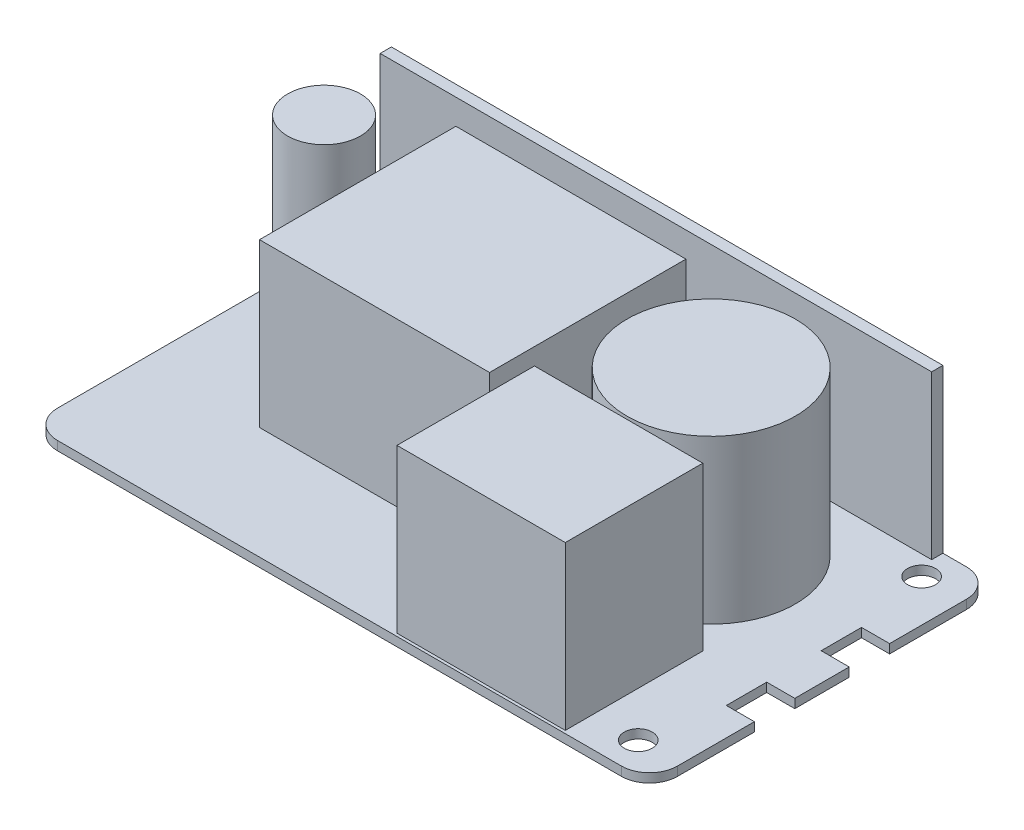
SolidWorks part; units mm, degrees
ref_plane "前视基准面" through (0, 0, 0) normal (0, 0, 1) x (1, 0, 0)
ref_plane "上视基准面" through (0, 0, 0) normal (0, 1, 0) x (1, 0, 0)
ref_plane "右视基准面" through (0, 0, 0) normal (1, 0, 0) x (0, 0, -1)
sketch "草图1" plane through (0, 0, 0) normal (0, 1, 0) x (1, 0, 0)
  line L0 (55.25, 12.05) -> (50.25, 12.05)
  line L1 (-50.25, 30.75) -> (50.25, 30.75)
  line L2 (-55.25, 25.75) -> (-55.25, -25.75)
  line L3 (-50.25, -30.75) -> (50.25, -30.75)
  line L4 (55.25, 25.75) -> (55.25, 12.05)
  line L5 (-55.25, 30.75) -> (55.25, -30.75) construction
  line L6 (-55.25, -30.75) -> (55.25, 30.75) construction
  line L7 (50.25, 12.05) -> (50.25, 4.85)
  line L8 (50.25, 4.85) -> (55.25, 4.85)
  line L9 (67.1485, 0) -> (0, 0) construction
  line L10 (50.25, -4.85) -> (55.25, -4.85)
  line L11 (50.25, -12.05) -> (50.25, -4.85)
  line L12 (55.25, -12.05) -> (50.25, -12.05)
  line L13 (55.25, 4.85) -> (55.25, -4.85)
  line L14 (55.25, -12.05) -> (55.25, -25.75)
  arc A0 (50.25, 30.75) -> (55.25, 25.75) centre (50.25, 25.75) cw
  arc A1 (50.25, -30.75) -> (55.25, -25.75) centre (50.25, -25.75) ccw
  arc A2 (-55.25, -25.75) -> (-50.25, -30.75) centre (-50.25, -25.75) ccw
  arc A3 (-50.25, 30.75) -> (-55.25, 25.75) centre (-50.25, 25.75) ccw
  point P0 (0, 0)
  dimension "D3" = 5
  dimension "D1" = 110.5
  dimension "D2" = 61.5
  dimension "D4" = 18.7
  dimension "D5" = 5
  dimension "D6" = 7.2
extrude "凸台-拉伸1" add sketch "草图1" along normal blind 1.6
sketch "草图2" plane through (0, 1.6, 0) normal (0, 1, 0) x (1, 0, 0)
  line L0 (55.25, 12.05) -> (55.25, 25.75) construction
  line L2 (50.25, 30.75) -> (-50.25, 30.75) construction
  line L3 (67.6553, 0) -> (0, 0) construction
  circle A0 centre (47.75, 25.25) radius 2.5
  circle A1 centre (47.75, -25.25) radius 2.5
  dimension "D1" = 7.5
  dimension "D2" = 5.5
extrude "切除-拉伸1" cut sketch "草图2" against normal blind 1.6
sketch "草图3" plane through (0, 1.6, 0) normal (0, 1, 0) x (1, 0, 0)
  line L0 (50.25, 30.75) -> (-50.25, 30.75) construction
  line L1 (55.25, 12.05) -> (55.25, 25.75) construction
  line L2 (-55.25, 25.75) -> (-55.25, -25.75) construction
  line L3 (-52.25, 30.75) -> (46.05, 30.75)
  line L4 (-52.25, 30.75) -> (-52.25, 28.75)
  line L5 (-52.25, 28.75) -> (46.05, 28.75)
  line L6 (46.05, 30.75) -> (46.05, 28.75)
  line L7 (-52.25, 30.75) -> (46.05, 28.75) construction
  line L8 (-52.25, 28.75) -> (46.05, 30.75) construction
  line L9 (55.25, -25.75) -> (55.25, -12.05) construction
  line L10 (9.75, -5.75) -> (39.75, -5.75)
  line L11 (9.75, -5.75) -> (9.75, -30.25)
  line L12 (9.75, -30.25) -> (39.75, -30.25)
  line L13 (39.75, -5.75) -> (39.75, -30.25)
  line L14 (9.75, -5.75) -> (39.75, -30.25) construction
  line L15 (9.75, -30.25) -> (39.75, -5.75) construction
  line L16 (-50.25, -30.75) -> (50.25, -30.75) construction
  line L18 (-34.25, 24.25) -> (6.75, 24.25)
  line L19 (-34.25, 24.25) -> (-34.25, -10.75)
  line L20 (-34.25, -10.75) -> (6.75, -10.75)
  line L21 (6.75, 24.25) -> (6.75, -10.75)
  line L22 (-34.25, 24.25) -> (6.75, -10.75) construction
  line L23 (-34.25, -10.75) -> (6.75, 24.25) construction
  circle A0 centre (25.75, 9.75) radius 15
  circle A1 centre (-47.75, 14.25) radius 6.5
  point P6 (-3.1, 29.75)
  point P13 (24.75, -18)
  point P22 (-13.75, 6.75)
  dimension "D1" = 21
  dimension "D2" = 29.5
  dimension "D13" = 16.5
  dimension "D14" = 7.5
  dimension "D3" = 2
  dimension "D4" = 98.3
  dimension "D5" = 3
  dimension "D6" = 24.5
  dimension "D7" = 30
  dimension "D8" = 15.5
  dimension "D9" = 35
  dimension "D10" = 41
  dimension "D11" = 20
  dimension "D12" = 21
  dimension "D15" = 0.5
extrude "凸台-拉伸2" add sketch "草图3" along normal blind 29
